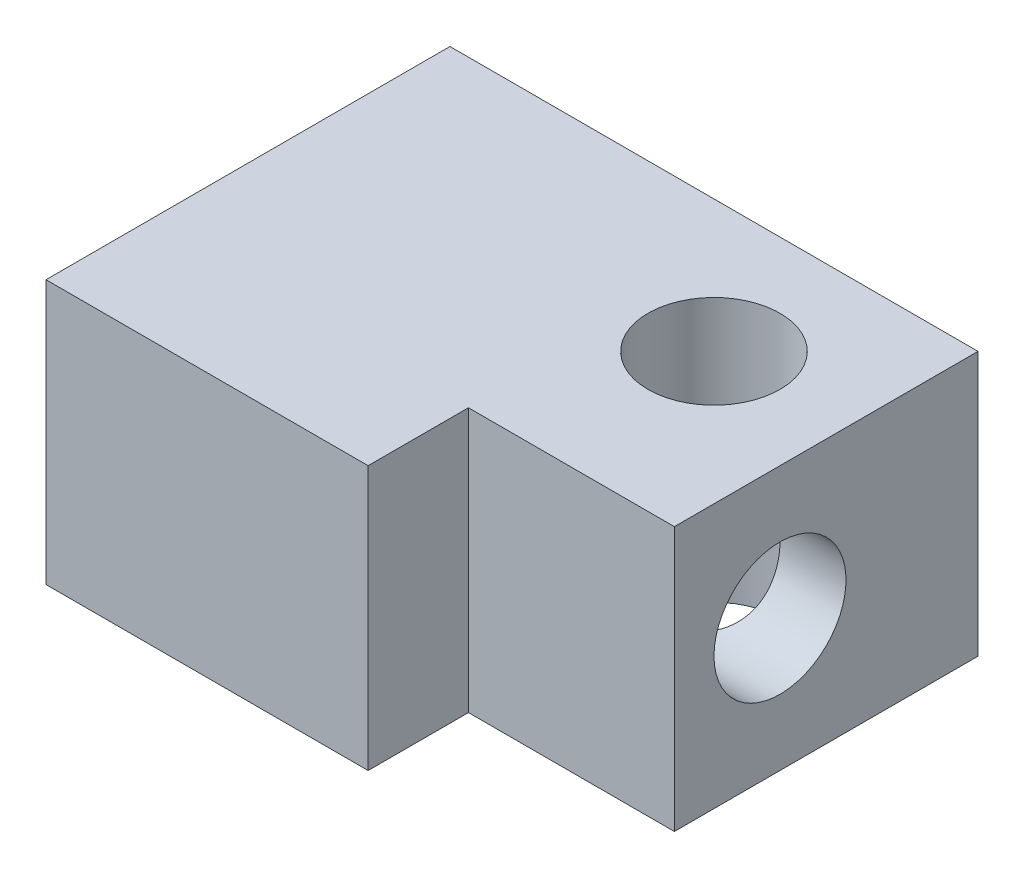
SolidWorks part; units mm, degrees
ref_plane "Front Plane" through (0, 0, 0) normal (0, 0, 1) x (1, 0, 0)
ref_plane "Top Plane" through (0, 0, 0) normal (0, 1, 0) x (1, 0, 0)
ref_plane "Right Plane" through (0, 0, 0) normal (1, 0, 0) x (0, 0, -1)
sketch "Sketch4" plane through (0, 0, 0) normal (0, 1, 0) x (1, 0, 0)
  line L5 (5, -86) -> (79, -86)
  line L11 (91.25, -2.5) -> (91.25, -88.5)
  line L12 (79, -5) -> (79, -7.5)
  line L13 (79, -83.5) -> (82.9, -83.5)
  line L14 (82.9, -82.1) -> (82.9, -83.5)
  line L15 (5, -83.5) -> (81.5, -83.5) construction
  line L16 (79, -88.5) -> (91.25, -88.5)
  line L17 (82.9, -82.1) -> (91.25, -82.1)
  line L18 (-4.75, -45.5) -> (91.25, -45.5)
  line L19 (79, -82.1) -> (91.25, -82.1) construction
  line L20 (79, -83.5) -> (79, -88.5)
  line L21 (79, -2.5) -> (91.25, -2.5)
  line L22 (79, -7.5) -> (79, -2.5)
  line L23 (79, -83.5) -> (91.25, -83.5) construction
  line L24 (79, -7.5) -> (82.9, -7.5)
  line L25 (5, -86) -> (81.5, -86) construction
  line L26 (82.9, -8.9) -> (91.25, -8.9)
  line L27 (82.9, -8.9) -> (82.9, -7.5)
  line L28 (43.25, -45.5) -> (43.25, -57.8047)
  line L30 (3.6, -10.15) -> (3.6, -8.25)
  line L32 (7.5, -8.25) -> (7.5, -2.5)
  line L33 (7.5, -2.5) -> (-2.5, -2.5)
  line L34 (7.5, -5) -> (79, -5)
  line L35 (-4.75, -45.5) -> (-4.75, -86)
  line L36 (5, -8.75) -> (5, -86)
  line L37 (7.5, -5) -> (79, -5) construction
  line L38 (-2.5, -2.5) -> (-2.5, -10.15)
  line L39 (3.6, -10.15) -> (-2.5, -10.15)
  line L40 (5, -8.75) -> (5, -86) construction
  line L41 (7.5, -8.25) -> (3.6, -8.25)
  circle A0 centre (5, -5) radius 1.25
  circle A1 centre (81.5, -5) radius 1.25
  circle A2 centre (81.5, -86) radius 1.25
  circle A3 centre (5, -86) radius 1.25
  point P4 (82.9, -5)
  point P7 (81.5, -86)
  point P8 (81.5, -5)
  point P27 (82.9, -86)
  point P41 (3.6, -7.5)
  point P42 (7.5, -7.5)
  point P47 (7.5, -8.75)
  point P48 (3.6, -8.75)
  dimension "D1" = 2
  dimension "D2" = 2
extrude "Boss-Extrude1" add sketch "Sketch4" along normal blind 5
sketch "Sketch5" plane through (-2.5, 0, 0) normal (-1, 0, 0) x (0, 0, 1)
  line L0 (2.5, 0) -> (2.5, 5)
  line L1 (6.25, 0) -> (6.25, 5)
  circle A0 centre (6.25, 2.5) radius 1.25
  dimension "D1" = 3.75
extrude "Cut-Extrude1" cut sketch "Sketch5" against normal blind 10 contours L1 A0 | L1 A0
